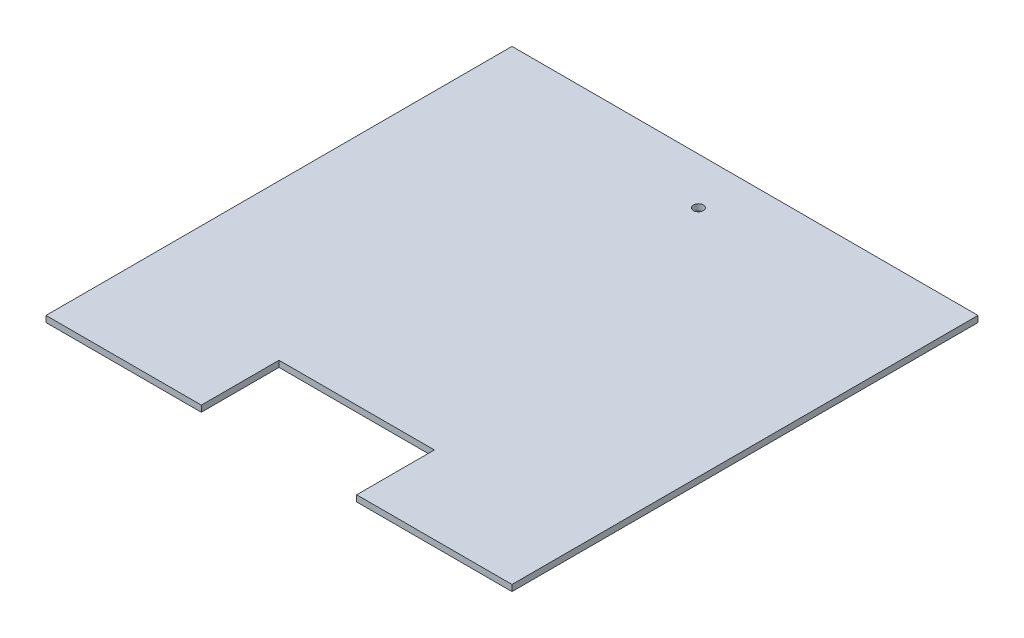
SolidWorks part; units mm, degrees
ref_plane "Front Plane" through (0, 0, 0) normal (0, 0, 1) x (1, 0, 0)
ref_plane "Top Plane" through (0, 0, 0) normal (0, 1, 0) x (1, 0, 0)
ref_plane "Right Plane" through (0, 0, 0) normal (1, 0, 0) x (0, 0, -1)
sketch "Sketch1" plane through (0, 0, 0) normal (0, 1, 0) x (1, 0, 0)
  line L1 (-95.25, -95.25) -> (95.25, -95.25)
  line L2 (-95.25, -95.25) -> (-95.25, 95.25)
  line L3 (-95.25, 95.25) -> (95.25, 95.25)
  line L4 (95.25, -95.25) -> (95.25, 95.25)
  line L5 (-95.25, -95.25) -> (95.25, 95.25) construction
  line L6 (-95.25, 95.25) -> (95.25, -95.25) construction
  point P0 (0, 0)
  dimension "D1" = 190.5
  dimension "D2" = 190.5
extrude "Boss-Extrude1" add sketch "Sketch1" along normal blind 2.54
sketch "Sketch2" plane through (0, 2.54, 0) normal (0, 1, 0) x (1, 0, 0)
  line L0 (-95.25, -95.25) -> (95.25, -95.25) construction
  line L1 (-31.75, -95.25) -> (31.75, -95.25)
  line L2 (-31.75, -95.25) -> (-31.75, -63.5)
  line L3 (-31.75, -63.5) -> (31.75, -63.5)
  line L4 (31.75, -95.25) -> (31.75, -63.5)
  line L5 (-31.75, -95.25) -> (31.75, -63.5) construction
  line L6 (-31.75, -63.5) -> (31.75, -95.25) construction
  line L7 (-95.25, 95.25) -> (-95.25, -95.25) construction
  line L8 (95.25, -95.25) -> (95.25, 95.25) construction
  point P0 (0, -79.375)
  dimension "D1" = 63.5
  dimension "D2" = 63.5
  dimension "D3" = 31.75
extrude "Cut-Extrude1" cut sketch "Sketch2" against normal blind 2.54
sketch "Sketch3" plane through (0, 2.54, 0) normal (0, 1, 0) x (1, 0, 0)
  circle A0 centre (0.0008, 76.1992) radius 2.032
extrude "Cut-Extrude2" cut sketch "Sketch3" against normal up to surface (2.54 mm away) up to face at (0, 0, 39.6875)
